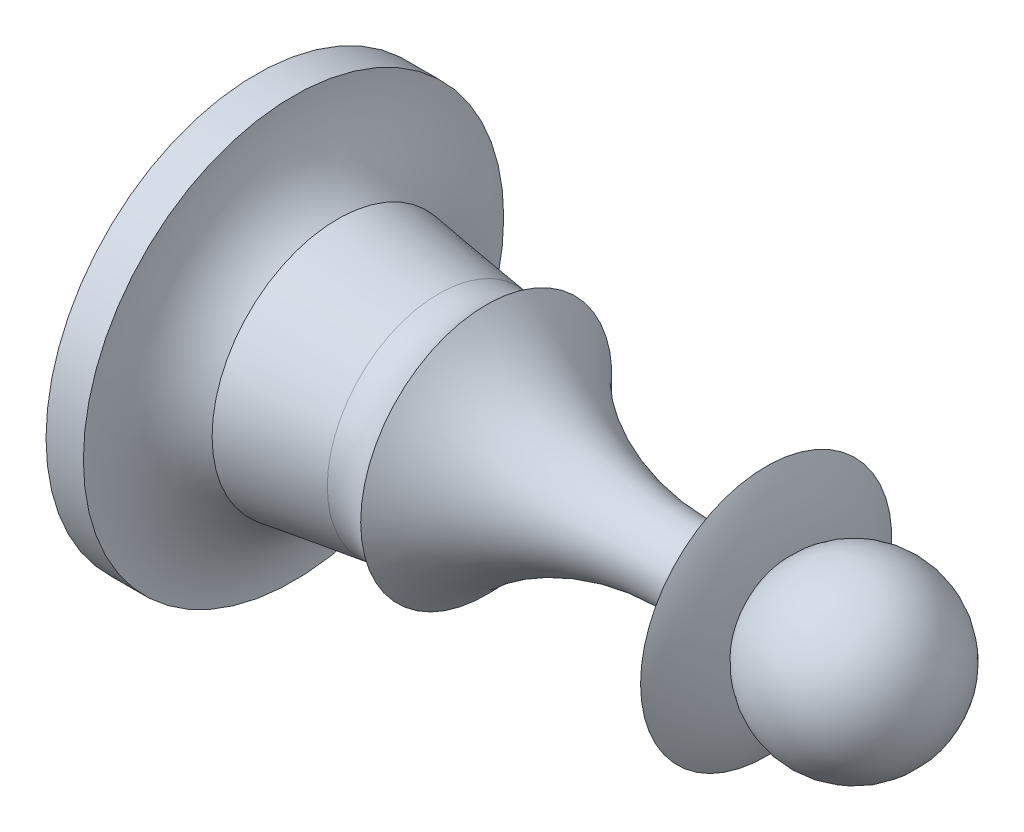
SolidWorks part; units mm, degrees
ref_plane "Front Plane" through (0, 0, 0) normal (0, 0, 1) x (1, 0, 0)
ref_plane "Top Plane" through (0, 0, 0) normal (0, 1, 0) x (1, 0, 0)
ref_plane "Right Plane" through (0, 0, 0) normal (1, 0, 0) x (0, 0, -1)
sketch "Sketch1" plane through (0, 0, 0) normal (0, 1, 0) x (1, 0, 0)
  line L0 (0, 0) -> (164.2058, 0) construction
  line L1 (0, 0) -> (0, 50.3356)
  line L2 (0, 50.3356) -> (8.9485, 50.3356)
  line L3 (19.5274, 30.0873) -> (43.7116, 26.6804)
  line L6 (0, 0) -> (164.2058, 0)
  arc A0 (8.9485, 50.3356) -> (19.5274, 30.0873) centre (33.6159, 50.3356) ccw
  arc A1 (43.7116, 26.6804) -> (55.1193, 30.0873) centre (45.7028, 40.8151) ccw
  arc A3 (117.226, 10.4698) -> (55.1193, 30.0873) centre (102.0801, 70.6398) cw
  arc A4 (117.226, 10.4698) -> (122.1477, 30.0873) centre (158.7838, 10.4698) cw
  arc A5 (127.3668, 13.8661) -> (122.1477, 30.0873) centre (88.9933, 10.4698) ccw
  arc A6 (127.3668, 13.8661) -> (164.2058, 0) centre (143.1767, 0) cw
revolve "Revolve3" add sketch "Sketch1" angle 360 about L0
